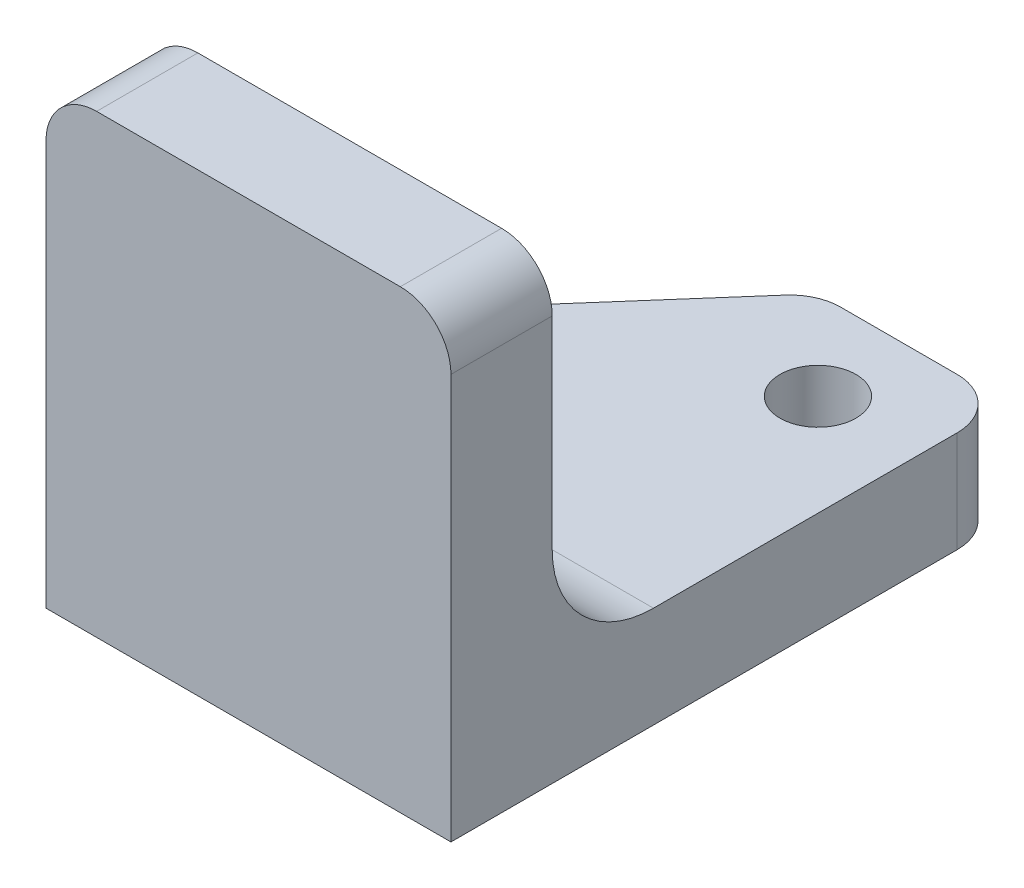
SolidWorks part; units mm, degrees
ref_plane "Front Plane" through (0, 0, 0) normal (0, 0, 1) x (1, 0, 0)
ref_plane "Top Plane" through (0, 0, 0) normal (0, 1, 0) x (1, 0, 0)
ref_plane "Right Plane" through (0, 0, 0) normal (1, 0, 0) x (0, 0, -1)
sketch "Sketch1" plane through (0, 0, 0) normal (0, 0, 1) x (1, 0, 0)
  line L0 (0, 0) -> (0, 16)
  line L1 (0, 0) -> (16, 0)
  line L2 (2, 18) -> (14, 18)
  line L3 (16, 0) -> (16, 16)
  arc A0 (0, 16) -> (2, 18) centre (2, 16) cw
  arc A1 (14, 18) -> (16, 16) centre (14, 16) cw
  point P7 (0, 18)
  point P10 (16, 18)
  dimension "D3" = 2
  dimension "D1" = 18
  dimension "D2" = 16
extrude "Boss-Extrude1" add sketch "Sketch1" along normal blind 4
sketch "Sketch2" plane through (0, 0, 0) normal (0, 1, 0) x (1, 0, 0)
  line L0 (16, -4) -> (16, 0) construction
  line L1 (0, 0) -> (16, 0)
  line L2 (0, 0) -> (0, 18)
  line L3 (0, 18) -> (16, 18)
  line L4 (16, 0) -> (16, 18)
  dimension "D1" = 18
extrude "Boss-Extrude2" add sketch "Sketch2" along normal blind 4
fillet "Fillet1" radius 4 1 edges
sketch "Sketch3" plane through (0, 4, 0) normal (0, 1, 0) x (1, 0, 0)
  line L0 (0, 18) -> (16, 4) construction
  line L1 (16, 18) -> (8, 11) construction
  line L4 (0, 18) -> (0, 4)
  line L5 (0, 4) -> (16, 4)
  line L8 (16, 4) -> (16, 18)
  line L9 (16, 18) -> (0, 18)
  line L10 (0, 18) -> (0, 4) construction
  line L11 (0, 4) -> (16, 4) construction
  line L12 (16, 4) -> (16, 18) construction
  line L13 (16, 18) -> (0, 18) construction
  circle A0 centre (12, 14.5) radius 1.5
  circle A1 centre (5.0619, 6.5708) radius 1.5
  dimension "D1" = 0
  dimension "D2" = 3
hole_wizard "Ø3.0 (3) Diameter Hole1" positions "Sketch4" profile "Sketch5" hole size "Ø3.0" standard "ANSI Metric"
sketch "Sketch4" plane through (939.6247, 4, -711.338) normal (0, 1, 0) x (-0.0418, 0, -0.9991)
  point P0 (-665.0679, 963.2181)
  point P3 (-657.4358, 955.9545)
sketch "Sketch5" plane through (5.0619, 4, -6.5708) normal (1, 0, 0) x (0, 0, 1)
  line L0 (0, 0) -> (0, 30.9013)
  line L1 (0, 30.9013) -> (1.5, 30)
  line L2 (1.5, 30) -> (1.5, 0)
  line L3 (1.5, 0) -> (0, 0)
  line L4 (0, 30.9013) -> (-1.5, 30) construction
  line L5 (0, -6.35) -> (0, 107.95) construction
  dimension "Hole Dia." = 3
  dimension "Hole Depth" = 30
  dimension "Drill Angle" = 118
sketch "Sketch6" plane through (0, 4, 0) normal (0, 1, 0) x (1, 0, 0)
  line L0 (8.4875, 18) -> (0, 8.3)
  line L1 (16, 18) -> (0, 18) construction
  line L2 (0, 18) -> (0, 4) construction
  line L3 (5.0619, 6.5708) -> (12, 14.5) construction
  line L4 (0, 8.3) -> (0, 18)
  line L5 (0, 18) -> (8.4875, 18)
extrude "Cut-Extrude1" cut sketch "Sketch6" against normal blind 10
fillet "Fillet2" radius 2 3 edges at (16, 2, -18) (0, 2, -8.3) (8.4875, 2, -18)
